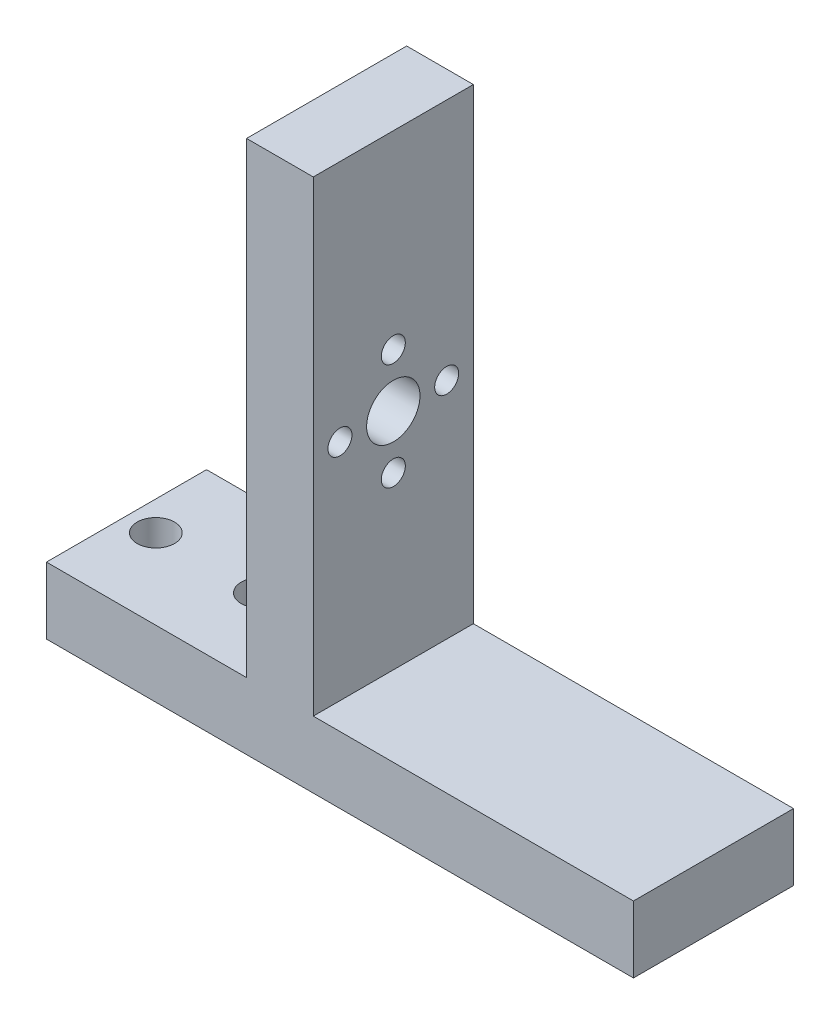
SolidWorks part; units mm, degrees
ref_plane "Front Plane" through (0, 0, 0) normal (0, 0, 1) x (1, 0, 0)
ref_plane "Top Plane" through (0, 0, 0) normal (0, 1, 0) x (1, 0, 0)
ref_plane "Right Plane" through (0, 0, 0) normal (1, 0, 0) x (0, 0, -1)
sketch "Sketch2" plane through (0, 0, 0) normal (0, 0, 1) x (1, 0, 0)
  line L0 (-27.94, 0) -> (27.94, 0)
  line L1 (27.94, 0) -> (27.94, 6.35)
  line L2 (27.94, 6.35) -> (-2.54, 6.35)
  line L3 (-2.54, 6.35) -> (-2.54, 50.8)
  line L4 (-2.54, 50.8) -> (-8.89, 50.8)
  line L5 (-8.89, 50.8) -> (-8.89, 6.35)
  line L6 (-8.89, 6.35) -> (-27.94, 6.35)
  line L7 (-27.94, 6.35) -> (-27.94, 0)
  dimension "D1" = 30.48
  dimension "D2" = 6.35
  dimension "D3" = 44.45
  dimension "D4" = 44.45
  dimension "D5" = 19.05
  dimension "D6" = 6.35
extrude "Boss-Extrude1" add sketch "Sketch2" along normal blind 15.24
sketch "Sketch5" plane through (-8.89, 0, 0) normal (-1, 0, 0) x (0, 0, 1)
  line L0 (15.24, 50.8) -> (0, 50.8) construction
  line L2 (0, 50.8) -> (0, 6.35) construction
  circle A0 centre (7.62, 32.766) radius 1.143
  circle A1 centre (7.62, 27.686) radius 2.54
  circle A2 centre (12.7, 27.686) radius 1.143
  circle A3 centre (7.62, 22.606) radius 1.143
  circle A4 centre (2.54, 27.686) radius 1.143
  point P14 (0, 0)
  point P15 (0, 0)
  dimension "D2" = 2.286
  dimension "D4" = 5.08
  dimension "D7" = 2.286
  dimension "D8" = 2.286
  dimension "D10" = 2.286
  dimension "D1" = 7.62
  dimension "0.71" = 18.034
  dimension "D3" = 5.08
  dimension "D5" = 7.62
  dimension "D6" = 5.08
  dimension "D9" = 5.08
  dimension "D11" = 5.08
extrude "Cut-Extrude1" cut sketch "Sketch5" against normal blind 15.24
sketch "Sketch6" plane through (0, 6.35, 0) normal (0, 1, 0) x (1, 0, 0)
  line L0 (-8.89, 0) -> (-27.94, 0) construction
  line L1 (-27.94, -15.24) -> (-27.94, 0) construction
  circle A0 centre (-25.146, -7.62) radius 1.778
  circle A1 centre (-15.24, -7.62) radius 1.778
  point P6 (0, 0)
  dimension "D1" = 3.556
  dimension "D3" = 3.556
  dimension "D2" = 9.906
  dimension "D4" = 7.62
  dimension "D5" = 2.794
extrude "Cut-Extrude2" cut sketch "Sketch6" against normal blind 15.24
